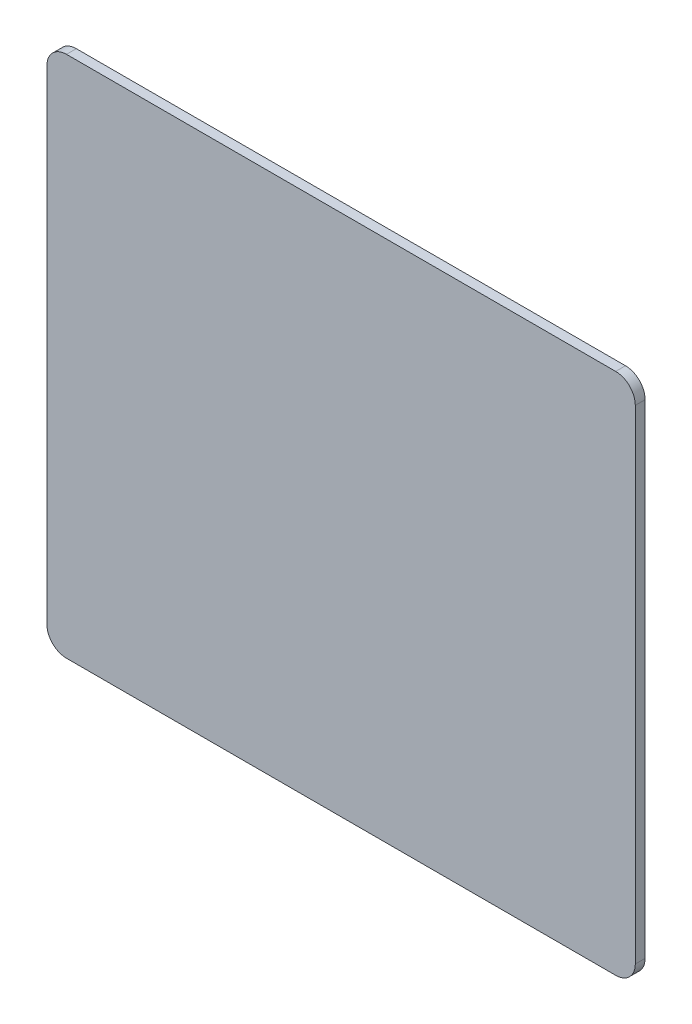
SolidWorks part; units mm, degrees
ref_plane "前视基准面" through (0, 0, 0) normal (0, 0, 1) x (1, 0, 0)
ref_plane "上视基准面" through (0, 0, 0) normal (0, 1, 0) x (1, 0, 0)
ref_plane "右视基准面" through (0, 0, 0) normal (1, 0, 0) x (0, 0, -1)
sketch "草图1" plane through (0, 0, 0) normal (0, 0, 1) x (1, 0, 0)
  line L0 (-56.8727, 0) -> (64.5183, 0) construction
  line L1 (0, 50.3001) -> (0, -55.129) construction
  line L3 (42, -40) -> (-42, -40)
  line L4 (45, -37) -> (45, 37)
  line L5 (42, 40) -> (-42, 40)
  line L6 (-45, -37) -> (-45, 37)
  line L7 (45, -40) -> (-45, 40) construction
  line L8 (45, 40) -> (-45, -40) construction
  arc A0 (42, 40) -> (45, 37) centre (42, 37) cw
  arc A1 (45, -37) -> (42, -40) centre (42, -37) cw
  arc A2 (-45, -37) -> (-42, -40) centre (-42, -37) ccw
  arc A3 (-45, 37) -> (-42, 40) centre (-42, 37) cw
  point P5 (0, 0)
  dimension "D3" = 3
  dimension "D1" = 90
  dimension "D2" = 80
extrude "凸台-拉伸1" add sketch "草图1" along normal blind 1.5
